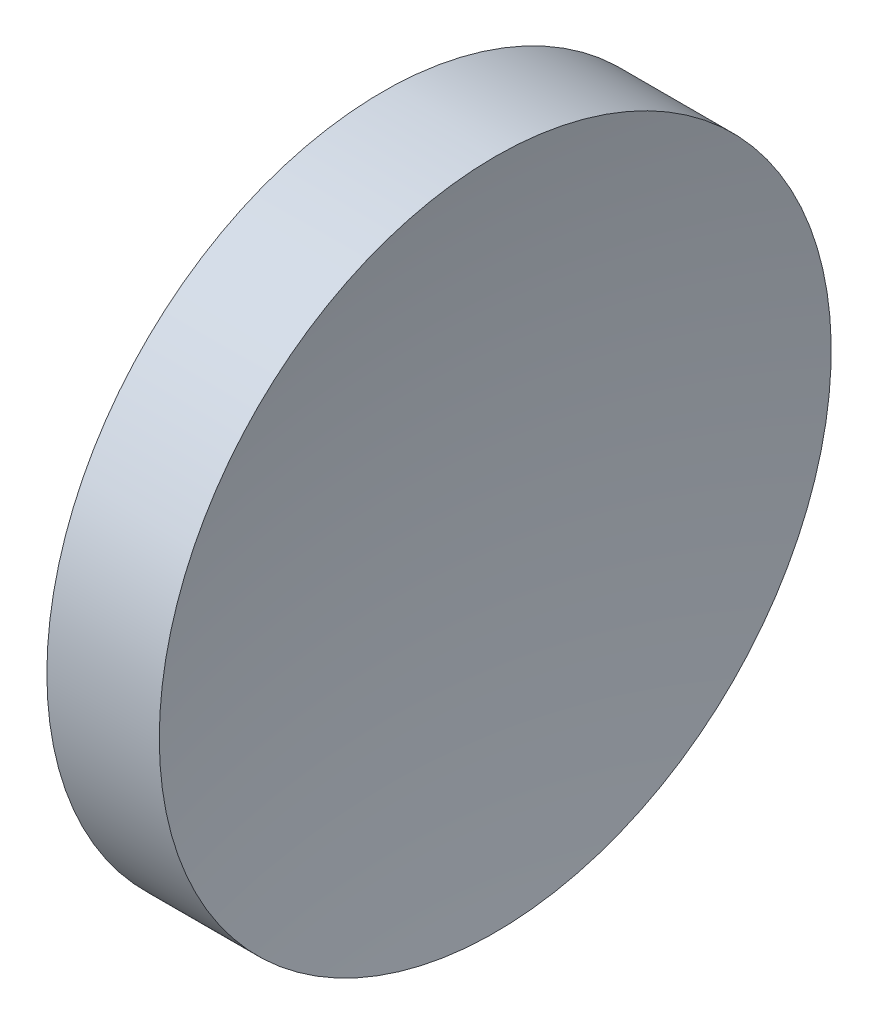
SolidWorks part; units mm, degrees
ref_plane "前视基准面" through (0, 0, 0) normal (0, 0, 1) x (1, 0, 0)
ref_plane "上视基准面" through (0, 0, 0) normal (0, 1, 0) x (1, 0, 0)
ref_plane "右视基准面" through (0, 0, 0) normal (1, 0, 0) x (0, 0, -1)
sketch "草图1" plane through (0, 0, 0) normal (0, 0, 1) x (1, 0, 0)
  line L0 (217.9703, 138.756) -> (265.5527, 138.756) construction
  line L1 (230.1996, 138.756) -> (230.1996, 176.256)
  line L2 (230.1996, 176.256) -> (242.7467, 176.256)
  line L3 (239.1996, 138.756) -> (230.1996, 138.756)
  arc A0 (242.7467, 176.256) -> (239.1996, 138.756) centre (439.1996, 138.756) ccw
  dimension "D1" = 200
  dimension "D2" = 12.5471
revolve "旋转1" add sketch "草图1" angle 360 about L0
